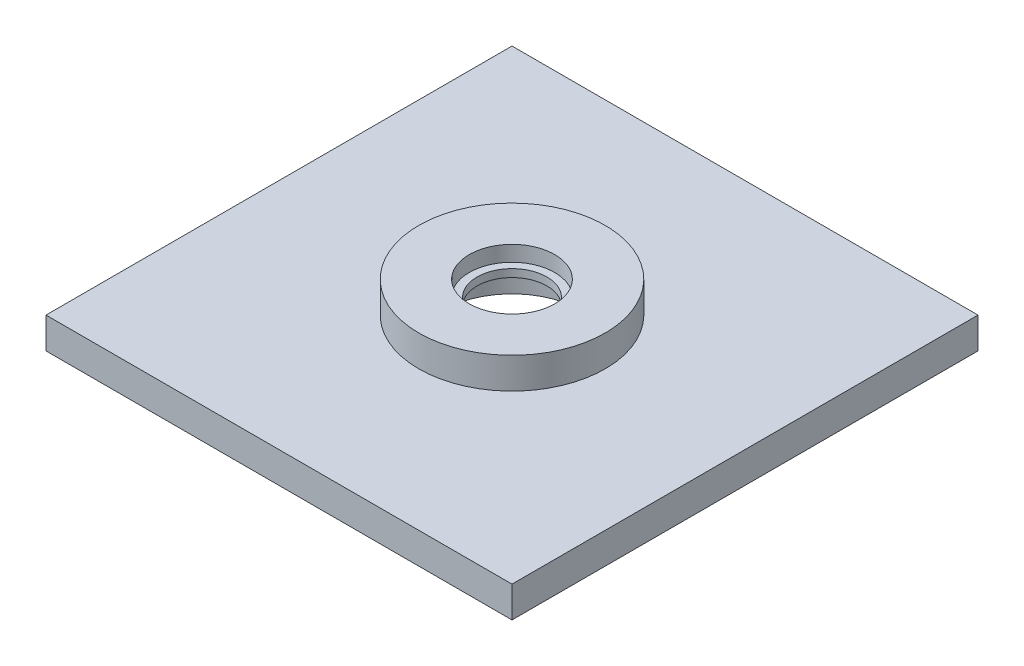
SolidWorks part; units mm, degrees
ref_plane "Front Plane" through (0, 0, 0) normal (0, 0, 1) x (1, 0, 0)
ref_plane "Top Plane" through (0, 0, 0) normal (0, 1, 0) x (1, 0, 0)
ref_plane "Right Plane" through (0, 0, 0) normal (1, 0, 0) x (0, 0, -1)
sketch "Sketch1" plane through (0, 0, 0) normal (0, 1, 0) x (1, 0, 0)
  line L1 (-47.625, 47.625) -> (47.625, 47.625)
  line L2 (-47.625, 47.625) -> (-47.625, -47.625)
  line L3 (-47.625, -47.625) -> (47.625, -47.625)
  line L4 (47.625, 47.625) -> (47.625, -47.625)
  line L5 (-47.625, 47.625) -> (47.625, -47.625) construction
  line L6 (-47.625, -47.625) -> (47.625, 47.625) construction
  circle A0 centre (0, 0) radius 7.1438
  point P0 (0, 0)
  dimension "D2" = 14.2875
  dimension "D1" = 95.25
extrude "Boss-Extrude1" add sketch "Sketch1" along normal blind 6.35
sketch "Sketch3" plane through (0, 6.35, 0) normal (0, 1, 0) x (1, 0, 0)
  circle A0 centre (0, 0) radius 19.05
  circle A1 centre (0, 0) radius 7.1438 construction
  circle A2 centre (0, 0) radius 7.1438
  dimension "D1" = 38.1
extrude "Boss-Extrude2" add sketch "Sketch3" along normal blind 6.35 contours A0
sketch "Sketch2" plane through (0, 0, 0) normal (0, -1, 0) x (1, 0, 0)
  circle A0 centre (0, 0) radius 14.2875
  dimension "D1" = 28.575
extrude "Cut-Extrude1" cut sketch "Sketch2" against normal blind 7.9375
sketch "Sketch4" plane through (0, 12.7, 0) normal (0, 1, 0) x (1, 0, 0)
  circle A0 centre (0, 0) radius 8.7312
  dimension "D1" = 17.4625
extrude "Cut-Extrude2" cut sketch "Sketch4" against normal blind 3.175
